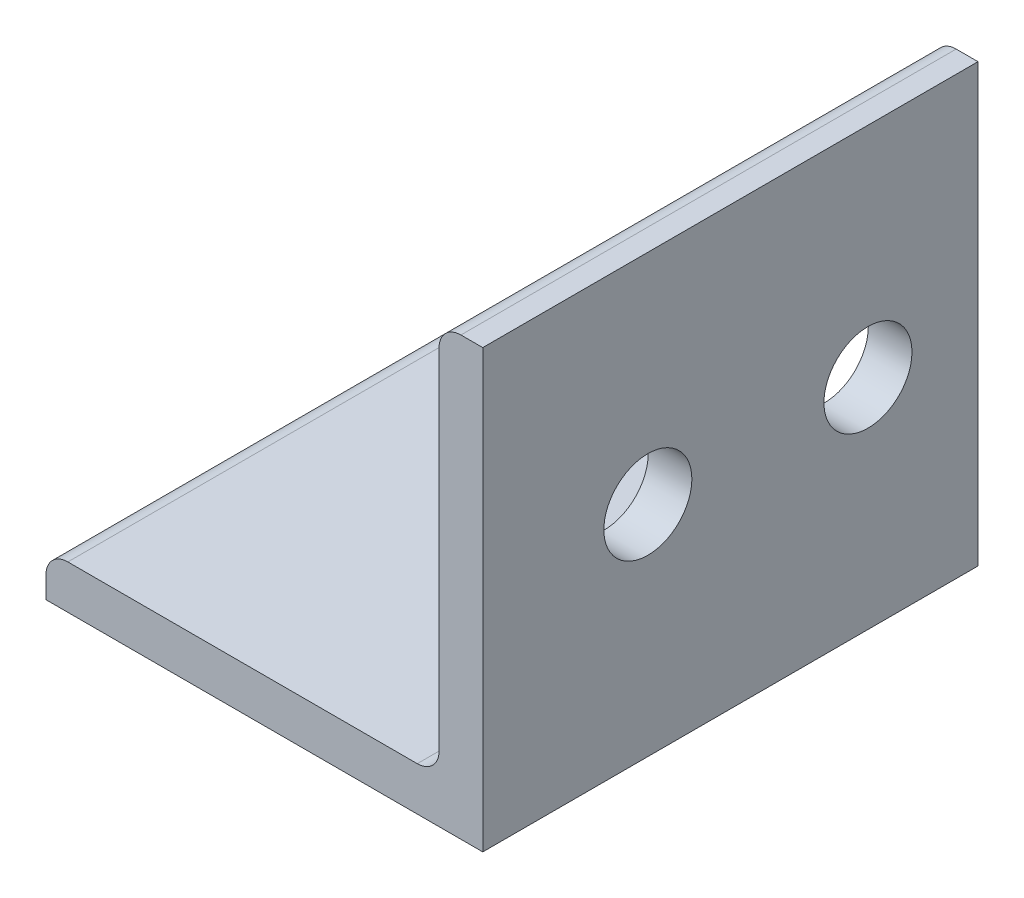
SolidWorks part; units mm, degrees
material "McMaster 6061-T6"
ref_plane "Front Plane" through (0, 0, 0) normal (0, 0, 1) x (1, 0, 0)
ref_plane "Top Plane" through (0, 0, 0) normal (0, 1, 0) x (1, 0, 0)
ref_plane "Right Plane" through (0, 0, 0) normal (1, 0, 0) x (0, 0, -1)
sketch "Sketch2" plane through (0, 0, 0) normal (0, 0, 1) x (1, 0, 0)
  line L0 (-7.9375, 0) -> (7.9375, 0)
  line L1 (7.9375, 0) -> (7.9375, 15.875)
  line L2 (7.9375, 15.875) -> (6.35, 15.875) construction
  line L3 (6.35, 15.0813) -> (6.35, 2.3812)
  line L4 (5.5563, 1.5875) -> (-7.1438, 1.5875)
  line L5 (-7.9375, 0) -> (-7.9375, 1.5875) construction
  line L6 (7.1438, 15.875) -> (7.9375, 15.875)
  line L7 (-7.9375, 0.7937) -> (-7.9375, 0)
  arc A0 (6.35, 15.0813) -> (7.1438, 15.875) centre (7.1438, 15.0813) cw
  arc A1 (-7.9375, 0.7937) -> (-7.1438, 1.5875) centre (-7.1438, 0.7937) cw
  arc A2 (6.35, 2.3812) -> (5.5563, 1.5875) centre (5.5563, 2.3812) cw
  dimension "Vert" = 15.875
  dimension "Horz" = 15.875
  dimension "Thickness" = 1.5875
extrude "Boss-Extrude1" add sketch "Sketch2" along normal mid plane 304.8
ref_plane "Contact Plane 1" through (0, 1.5875, 0) normal (0, 1, 0) x (1, 0, 0)
ref_plane "Contact Plane 2" through (6.35, 0, 0) normal (-1, 0, 0) x (0, 0, 1)
sketch "Sketch3" plane through (7.9375, 0, 0) normal (1, 0, 0) x (0, 0, -1)
  line L0 (131.5135, 7.9375) -> (139.5135, 7.9375) construction
  line L2 (152.4, 0) -> (152.4, 15.875) construction
  point P4 (152.4, 7.9375)
  line B0 (152.84, 14.6375) -> (136.4, 14.6375)
  line B1 (136.4, 14.6375) -> (136.4, 11.9375)
  line B2 (136.4, 11.9375) -> (134.4, 11.9375)
  line B3 (134.4, 11.9375) -> (134.4, 3.9375)
  line B4 (134.4, 3.9375) -> (136.4, 3.9375)
  line B5 (136.4, 3.9375) -> (136.4, 1.2375)
  line B6 (136.4, 1.2375) -> (152.84, 1.2375)
  line B7 (152.84, 1.2375) -> (152.84, 3.0375)
  line B8 (152.84, 3.0375) -> (158.4, 3.0375)
  line B9 (158.4, 3.0375) -> (158.4, 4.9375)
  line B10 (158.4, 4.9375) -> (152.4, 4.9375)
  line B11 (152.4, 4.9375) -> (152.4, 10.9375)
  line B12 (152.4, 10.9375) -> (158.4, 10.9375)
  line B13 (158.4, 10.9375) -> (158.4, 12.8375)
  line B14 (158.4, 12.8375) -> (152.84, 12.8375)
  line B15 (152.84, 12.8375) -> (152.84, 14.6375)
  circle B16 centre (148.4, 7.9375) radius 1.6
  circle B17 centre (140.4, 7.9375) radius 1.6
sketch_block_instance "Block-CableMounting-1"
sketch_block "Block-CableMounting"
extrude "Cut-Extrude1" cut sketch "Sketch3" against normal up to next contours B16 L0 | L0 B16 | B17 L0 | L0 B17
ref_point "Point1"
sketch "Sketch4" plane through (0, 0, 152.4) normal (0, 0, 1) x (1, 0, 0)
  line L6 (-7.9375, 0.7937) -> (-7.9375, 0)
  line L7 (-7.9375, 0) -> (7.9375, 0)
  line L8 (7.9375, 0) -> (7.9375, 15.875)
  line L9 (7.9375, 15.875) -> (7.1438, 15.875)
  line L10 (6.35, 15.0813) -> (6.35, 2.3812)
  line L11 (5.5563, 1.5875) -> (-7.1438, 1.5875)
  line L12 (-7.9375, 0.7937) -> (-7.9375, 0)
  line L13 (-7.9375, 0) -> (7.9375, 0)
  line L14 (7.9375, 0) -> (7.9375, 15.875)
  line L15 (7.9375, 15.875) -> (7.1438, 15.875)
  line L16 (6.35, 15.0813) -> (6.35, 2.3812)
  line L17 (5.5563, 1.5875) -> (-7.1438, 1.5875)
  arc A3 (7.1438, 15.875) -> (6.35, 15.0813) centre (7.1438, 15.0813) ccw
  arc A4 (5.5563, 1.5875) -> (6.35, 2.3812) centre (5.5563, 2.3812) ccw
  arc A5 (-7.1438, 1.5875) -> (-7.9375, 0.7937) centre (-7.1438, 0.7937) ccw
  arc A6 (7.1438, 15.875) -> (6.35, 15.0813) centre (7.1438, 15.0813) ccw
  arc A7 (5.5563, 1.5875) -> (6.35, 2.3812) centre (5.5563, 2.3812) ccw
  arc A8 (-7.1438, 1.5875) -> (-7.9375, 0.7937) centre (-7.1438, 0.7937) ccw
  dimension "D1" = 0
extrude "Cut-Extrude2" cut sketch "Sketch4" against normal up to vertex (286.8 mm away)
sketch "Sketch5" plane through (0, 0, 0) normal (0, -1, 0) x (1, 0, 0)
  line L0 (7.9375, -152.4) -> (-7.9375, -134.4) construction
  line L4 (7.9375, -134.4) -> (-7.9375, -134.4)
  line L5 (-7.9375, -134.4) -> (-7.9375, -152.4)
  line L6 (-7.9375, -152.4) -> (7.9375, -152.4)
  line L7 (7.9375, -152.4) -> (7.9375, -134.4)
  line L8 (7.9375, -134.4) -> (-7.9375, -134.4) construction
  line L9 (-7.9375, -134.4) -> (-7.9375, -152.4) construction
  line L10 (-7.9375, -152.4) -> (7.9375, -152.4) construction
  line L11 (7.9375, -152.4) -> (7.9375, -134.4) construction
  circle A0 centre (0, -143.4) radius 1.5875
  dimension "D2" = 3.175
  dimension "D1" = 0
extrude "Cut-Extrude3" cut sketch "Sketch5" against normal up to next
